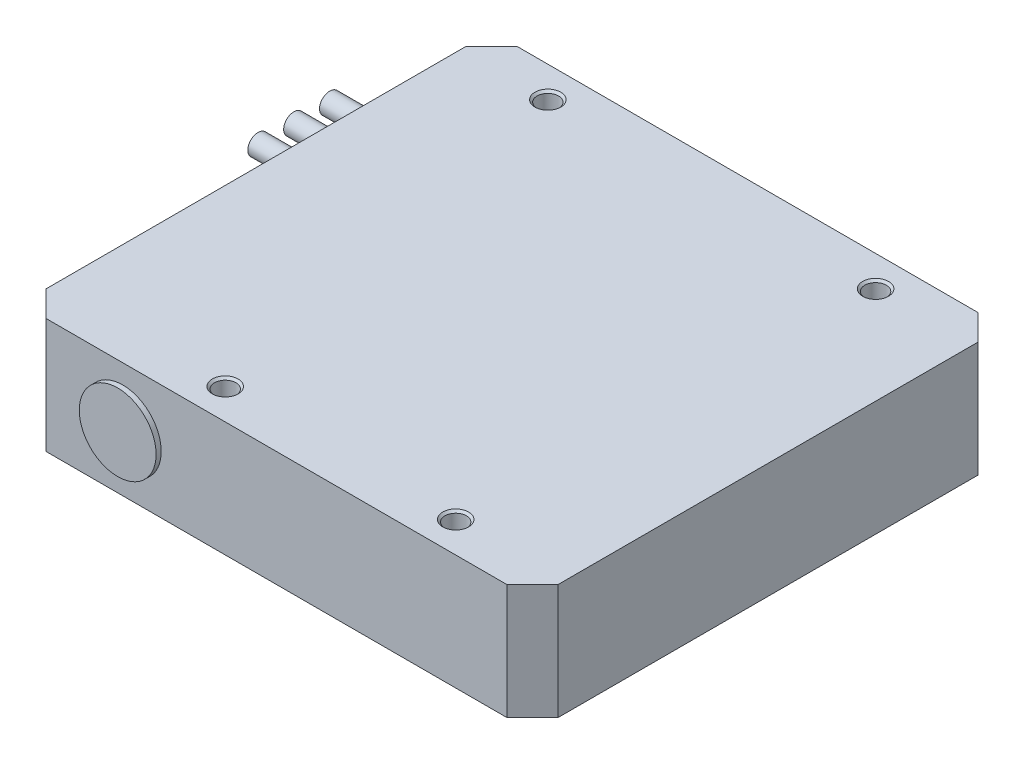
SolidWorks part; units mm, degrees
ref_plane "Front Plane" through (0, 0, 0) normal (0, 0, 1) x (1, 0, 0)
ref_plane "Top Plane" through (0, 0, 0) normal (0, 1, 0) x (1, 0, 0)
ref_plane "Right Plane" through (0, 0, 0) normal (1, 0, 0) x (0, 0, -1)
sketch "Sketch1" plane through (0, 0, 0) normal (0, 1, 0) x (1, 0, 0)
  line L1 (-50, -46) -> (50, -46)
  line L2 (-50, -46) -> (-50, 46)
  line L3 (-50, 46) -> (50, 46)
  line L4 (50, -46) -> (50, 46)
  line L5 (-50, -46) -> (50, 46) construction
  line L6 (-50, 46) -> (50, -46) construction
  point P0 (0, 0)
  dimension "D1" = 100
  dimension "D2" = 92
extrude "Boss-Extrude1" add sketch "Sketch1" along normal blind 22.5
chamfer "Chamfer1" distance 5 4 edges at (50, 11.25, -46) (-50, 11.25, -46) (-50, 11.25, 46) (50, 11.25, 46)
sketch "Sketch3" plane through (0, 0, 46) normal (0, 0, 1) x (1, 0, 0)
  line L0 (-30, 22.5) -> (-30, 0) construction
  line L1 (-45, 22.5) -> (45, 22.5) construction
  line L2 (50.6, 0) -> (-50.6, 0) construction
  line L3 (-45, 22.5) -> (-45, 0) construction
  circle A0 centre (-30, 11.25) radius 7.5
  dimension "D1" = 15
  dimension "D2" = 15
extrude "Boss-Extrude2" add sketch "Sketch3" along normal blind 1
sketch "Sketch4" plane through (0, 22.5, 0) normal (0, 1, 0) x (1, 0, 0)
  line L0 (-45, -46) -> (45, -46) construction
  line L1 (50, -41) -> (50, 41) construction
  line L2 (45, 46) -> (-45, 46) construction
  point P0 (-16, -40)
  point P3 (29, -40)
  point P6 (-33, 40)
  point P8 (31, 40)
  point P10 (0, 0)
  point P11 (0, 0)
  dimension "D1" = 6
  dimension "D2" = 21
  dimension "D3" = 45
  dimension "D4" = 6
  dimension "D5" = 19
  dimension "D6" = 64
hole_wizard "M5 Tapped Hole1" positions "Sketch5" profile "Sketch7" tap size "M5" standard "ISO"
sketch "Sketch5" plane through (0, 22.5, 0) normal (0, 1, 0) x (1, 0, 0)
  point P0 (-33, 40)
  point P3 (31, 40)
  point P6 (29, -40)
  point P9 (-16, -40)
cosmetic thread "Hole Thread1" parameters "D2"=5
cosmetic thread "Hole Thread2" parameters "D2"=5
cosmetic thread "Hole Thread3" parameters "D2"=5
cosmetic thread "Hole Thread4" parameters "D2"=5
sketch "Sketch7" plane through (-33, 22.5, -40) normal (1, 0, 0) x (0, 0, 1)
  line L0 (0, 0) -> (0, 6.2618)
  line L1 (0, 6.2618) -> (2.1, 5)
  line L2 (2.1, 5) -> (2.1, 0.425)
  line L3 (2.1, 0.425) -> (2.525, 0)
  line L5 (2.525, 0) -> (0, 0)
  line L6 (-2.1, 0.425) -> (-2.525, 0) construction
  line L10 (0, 6.2618) -> (-2.1, 5) construction
  line L11 (0, -6.35) -> (0, 107.95) construction
  dimension "Tap Drill Dia." = 4.2
  dimension "Tap Drill Depth" = 5
  dimension "Near C'Sink Dia." = 5.05
  dimension "Near C'Sink Angle" = 90
  dimension "Drill Angle" = 118
sketch "Sketch8" plane through (-50, 0, 0) normal (-1, 0, 0) x (0, 0, 1)
  line L0 (-35.4909, 22.5) -> (-35.4909, 0) construction
  line L1 (-41, 22.5) -> (41, 22.5) construction
  line L2 (-41, 0) -> (41, 0) construction
  line L3 (-29.4079, 11.25) -> (-22.4079, 11.25) construction
  line L4 (-22.4079, 11.25) -> (-15.4079, 11.25) construction
  circle A0 centre (-29.4079, 11.25) radius 2
  circle A1 centre (-22.4079, 11.25) radius 2
  circle A2 centre (-15.4079, 11.25) radius 2
  point P12 (-35.4909, 11.25)
  dimension "D1" = 4
  dimension "D2" = 7
extrude "Boss-Extrude3" add sketch "Sketch8" along normal blind 15
